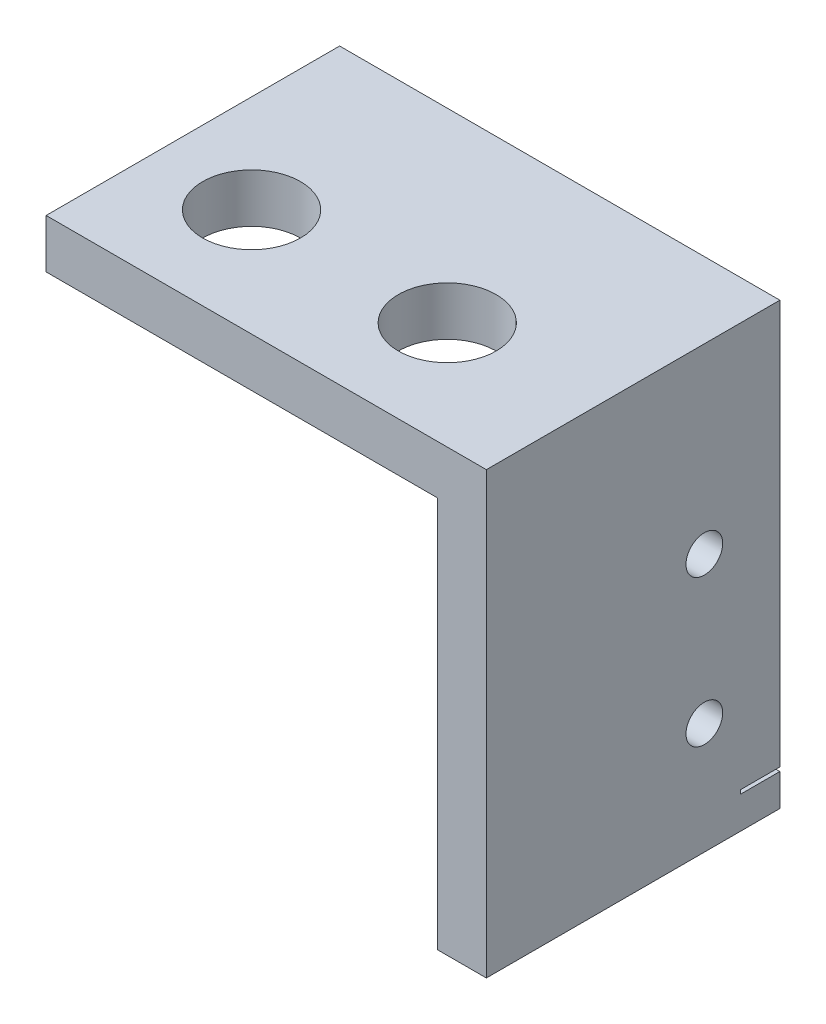
SolidWorks part; units mm, degrees
ref_plane "Front Plane" through (0, 0, 0) normal (0, 0, 1) x (1, 0, 0)
ref_plane "Top Plane" through (0, 0, 0) normal (0, 1, 0) x (1, 0, 0)
ref_plane "Right Plane" through (0, 0, 0) normal (1, 0, 0) x (0, 0, -1)
sketch "Sketch1" plane through (0, 0, 0) normal (0, 0, 1) x (1, 0, 0)
  line L1 (0, 0) -> (-28.575, 0)
  line L2 (0, 0) -> (0, 3.175)
  line L3 (0, 3.175) -> (-28.575, 3.175)
  line L4 (-28.575, 0) -> (-28.575, 3.175)
  line L5 (0, 0) -> (-3.175, 0)
  line L6 (0, 0) -> (0, -25.4)
  line L7 (0, -25.4) -> (-3.175, -25.4)
  line L8 (-3.175, 0) -> (-3.175, -25.4)
  dimension "D1" = 3.175
  dimension "D2" = 3.175
  dimension "D3" = 28.575
  dimension "D4" = 28.575
extrude "Boss-Extrude1" add sketch "Sketch1" along normal blind 19.05 contours L4 L1 L2 L3 | L1 L8 L7 L6
sketch "Sketch2" plane through (-3.175, 0, 0) normal (-1, 0, 0) x (0, 0, 1)
  line L0 (0, 0) -> (0, -25.4) construction
  line L1 (0, -25.4) -> (19.05, -25.4) construction
  line L2 (19.05, -25.4) -> (19.05, 0) construction
  line L3 (19.05, 0) -> (0, 0) construction
  line L4 (0, -8.636) -> (19.05, -8.636) construction
  line L5 (0, -18.161) -> (19.05, -18.161) construction
  line L6 (4.9022, -8.636) -> (4.9022, -18.161) construction
  line L8 (0, -23.0632) -> (2.54, -23.0632)
  line L9 (0, -23.0632) -> (0, -23.3172)
  line L10 (0, -23.3172) -> (2.54, -23.3172)
  line L11 (2.54, -23.0632) -> (2.54, -23.3172)
  circle A0 centre (4.9022, -8.636) radius 1.1906
  circle A1 centre (4.9022, -18.161) radius 1.1906
  dimension "D4" = 2.3813
  dimension "D5" = 2.3813
  dimension "D1" = 8.636
  dimension "D2" = 9.525
  dimension "D3" = 4.9022
  dimension "D6" = 4.9022
  dimension "D7" = 5.1562
  dimension "D8" = 2.54
extrude "Switch Mount" cut sketch "Sketch2" against normal up to next
sketch "Sketch3" plane through (0, 0, 0) normal (0, -1, 0) x (1, 0, 0)
  line L0 (-3.175, 0) -> (-3.175, 19.05) construction
  line L1 (-3.175, 19.05) -> (-28.575, 19.05) construction
  line L2 (-28.575, 19.05) -> (-28.575, 0) construction
  line L3 (-28.575, 0) -> (-3.175, 0) construction
  line L4 (-3.175, 12.065) -> (-28.575, 12.065) construction
  circle A0 centre (-9.525, 12.065) radius 3.175
  circle A1 centre (-22.225, 12.065) radius 3.175
  point P16 (-18.4016, 9.525)
  point P17 (-19.2725, 9.949)
  dimension "D1" = 6.35
  dimension "D2" = 6.35
  dimension "D3" = 6.35
  dimension "D4" = 12.7
  dimension "D5" = 12.065
extrude "Bracket Mount" cut sketch "Sketch3" against normal up to next
